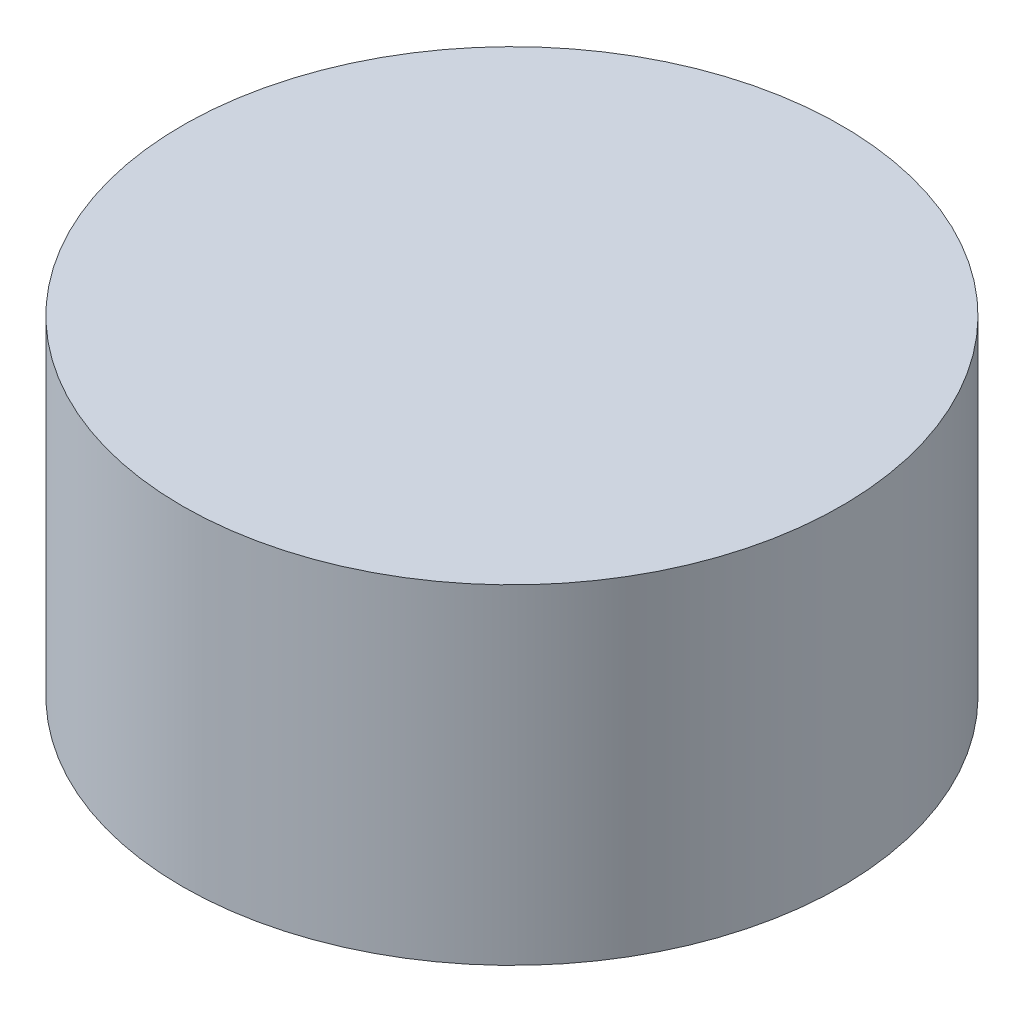
SolidWorks part; units mm, degrees
ref_plane "Front Plane" through (0, 0, 0) normal (0, 0, 1) x (1, 0, 0)
ref_plane "Top Plane" through (0, 0, 0) normal (0, 1, 0) x (1, 0, 0)
ref_plane "Right Plane" through (0, 0, 0) normal (1, 0, 0) x (0, 0, -1)
sketch "Sketch1" plane through (0, 0, 0) normal (0, 1, 0) x (1, 0, 0)
  circle A0 centre (0, 0) radius 10
extrude "Boss-Extrude1" add sketch "Sketch1" along normal blind 10
